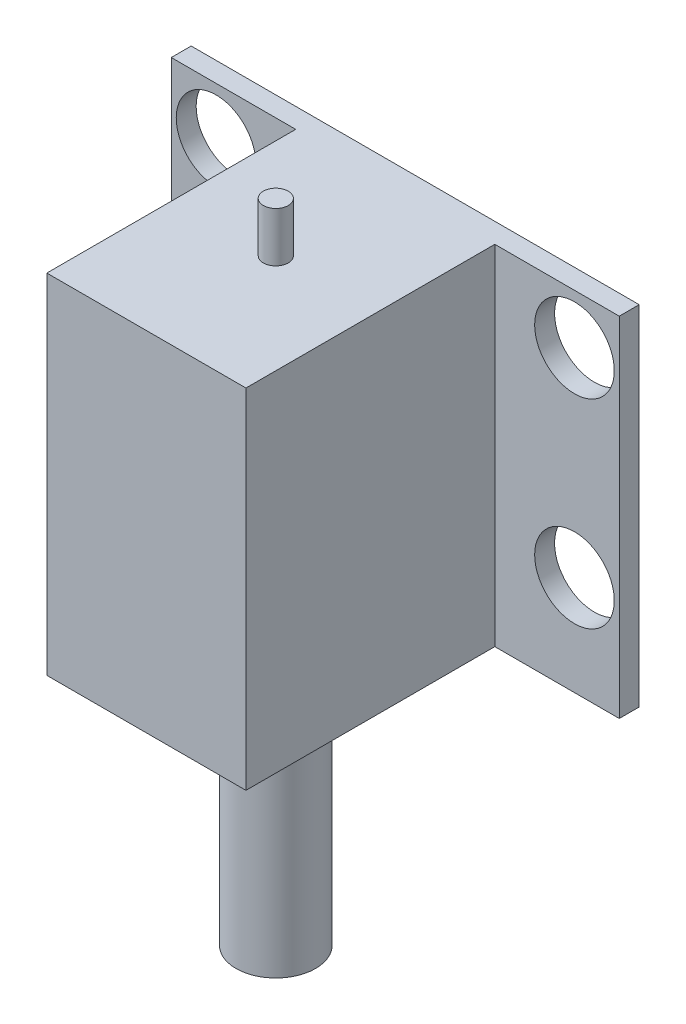
SolidWorks part; units mm, degrees
ref_plane "正面" through (0, 0, 0) normal (0, 0, 1) x (1, 0, 0)
ref_plane "平面" through (0, 0, 0) normal (0, 1, 0) x (1, 0, 0)
ref_plane "右側面" through (0, 0, 0) normal (1, 0, 0) x (0, 0, -1)
sketch "ｽｹｯﾁ1" plane through (0, 0, 0) normal (0, 0, 1) x (1, 0, 0)
  line L1 (-22.5, -17.5) -> (22.5, -17.5)
  line L2 (-22.5, -17.5) -> (-22.5, 17.5)
  line L3 (-22.5, 17.5) -> (22.5, 17.5)
  line L4 (22.5, -17.5) -> (22.5, 17.5)
  line L5 (-22.5, -17.5) -> (22.5, 17.5) construction
  line L6 (-22.5, 17.5) -> (22.5, -17.5) construction
  point P0 (0, 0)
  dimension "D1" = 45
  dimension "D2" = 35
extrude "ﾎﾞｽ - 押し出し1" add sketch "ｽｹｯﾁ1" along normal blind 2
sketch "ｽｹｯﾁ2" plane through (0, 0, 2) normal (0, 0, 1) x (1, 0, 0)
  line L0 (22.5, 17.5) -> (-22.5, 17.5) construction
  line L1 (10, -17.5) -> (-10, -17.5)
  line L2 (10, -17.5) -> (10, 17.5)
  line L3 (10, 17.5) -> (-10, 17.5)
  line L4 (-10, -17.5) -> (-10, 17.5)
  line L5 (10, -17.5) -> (-10, 17.5) construction
  line L6 (10, 17.5) -> (-10, -17.5) construction
  point P0 (0, 0)
  dimension "D1" = 20
extrude "ﾎﾞｽ - 押し出し2" add sketch "ｽｹｯﾁ2" along normal blind 25
sketch "ｽｹｯﾁ3" plane through (0, -17.5, 0) normal (0, -1, 0) x (-1, 0, 0)
  line L0 (-10, -2) -> (-22.5, -2) construction
  circle A0 centre (0, -14) radius 4
  dimension "D1" = 8
  dimension "D2" = 12
extrude "ﾎﾞｽ - 押し出し3" add sketch "ｽｹｯﾁ3" along normal blind 25
sketch "ｽｹｯﾁ4" plane through (0, 17.5, 0) normal (0, 1, 0) x (1, 0, 0)
  line L0 (-10, -2) -> (-22.5, -2) construction
  circle A0 centre (0, -14) radius 1.25
  dimension "D1" = 2.5
  dimension "D2" = 12
extrude "ﾎﾞｽ - 押し出し4" add sketch "ｽｹｯﾁ4" along normal blind 5
sketch "ｽｹｯﾁ5" plane through (0, 0, 0) normal (0, 0, -1) x (-1, 0, 0)
  line L0 (-22.5, 17.5) -> (22.5, 17.5) construction
  line L2 (22.5, 17.5) -> (22.5, -17.5) construction
  line L3 (0, 17.5) -> (0, -17.5)
  line L4 (22.5, -17.5) -> (-22.5, -17.5) construction
  circle A0 centre (18, 12.5) radius 4
  circle A1 centre (18, -7.5) radius 4
  circle A2 centre (-18, -7.5) radius 4
  circle A3 centre (-18, 12.5) radius 4
  dimension "D1" = 8
  dimension "D4" = 8
  dimension "D2" = 5
  dimension "D3" = 4.5
  dimension "D5" = 20
extrude "ｶｯﾄ - 押し出し1" cut sketch "ｽｹｯﾁ5" against normal through all contours A1 | A0 | A3 | A2
